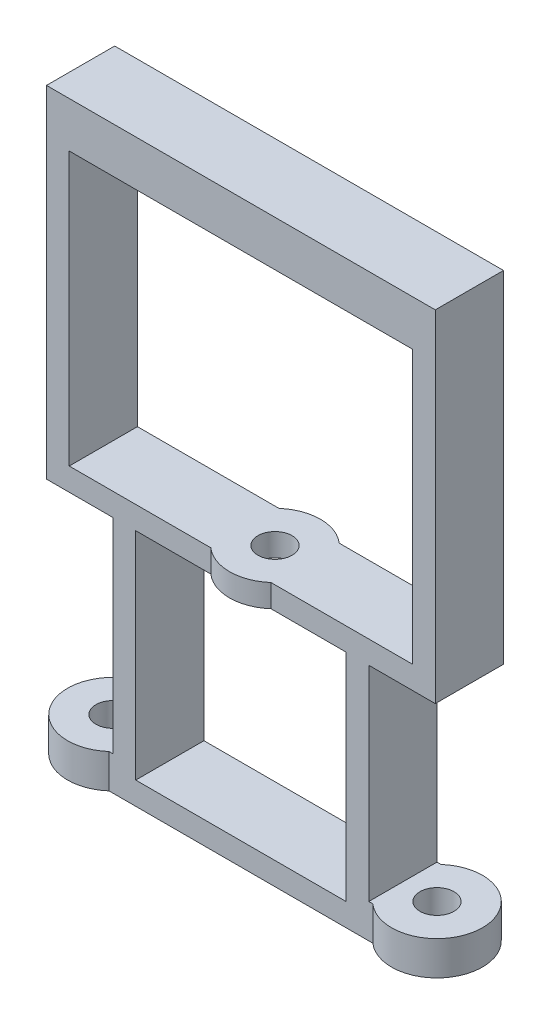
SolidWorks part; units mm, degrees
ref_plane "Front Plane" through (0, 0, 0) normal (0, 0, 1) x (1, 0, 0)
ref_plane "Top Plane" through (0, 0, 0) normal (0, 1, 0) x (1, 0, 0)
ref_plane "Right Plane" through (0, 0, 0) normal (1, 0, 0) x (0, 0, -1)
sketch "Sketch1" plane through (0, 0, 0) normal (0, 1, 0) x (1, 0, 0)
  line L0 (0, 0) -> (1.5, 0)
  line L1 (-55, 0) -> (55, 0) construction
  line L3 (2.6458, 3) -> (25.8542, 3)
  line L4 (27, 0) -> (28.5, 0)
  line L6 (25.8542, -3) -> (2.6458, -3)
  circle A0 centre (0, 0) radius 1.5
  circle A1 centre (28.5, 0) radius 1.5
  arc A2 (2.6458, 3) -> (2.6458, -3) centre (0, 0) ccw
  arc A3 (25.8542, -3) -> (31.1458, 3) centre (28.5, 0) ccw
  arc A4 (25.8542, -3) -> (25.8542, 3) centre (28.5, 0) ccw
  dimension "D2" = 3
  dimension "D3" = 3
  dimension "D5" = 8
  dimension "D8" = 8
  dimension "D1" = 28.5
  dimension "D4" = 6
  dimension "D7" = 3
extrude "Boss-Extrude1" add sketch "Sketch1" along normal blind 3
sketch "Sketch2" plane through (0, 3, 0) normal (0, 1, 0) x (1, 0, 0)
  line L0 (2.6458, 3) -> (25.8542, 3) construction
  line L1 (3, 3) -> (25.5, 3)
  line L2 (3, 3) -> (3, -3)
  line L3 (3, -3) -> (25.5, -3)
  line L4 (25.5, 3) -> (25.5, -3)
  line L5 (25.8542, -3) -> (2.6458, -3) construction
  circle A0 centre (28.5, 0) radius 1.5 construction
  dimension "D1" = 3
  dimension "D2" = 3
extrude "Boss-Extrude2" add sketch "Sketch2" along normal blind 20
sketch "Sketch3" plane through (0, 0, 3) normal (0, 0, 1) x (1, 0, 0)
  line L0 (3, 23) -> (25.5, 23) construction
  line L1 (5, 2) -> (23.5, 2)
  line L2 (5, 2) -> (5, 21)
  line L3 (5, 21) -> (23.5, 21)
  line L4 (23.5, 2) -> (23.5, 21)
  line L5 (3, 23) -> (3, 3) construction
  line L6 (25.5, 23) -> (25.5, 3) construction
  line L7 (25.8542, 3) -> (25.5, 3) construction
  dimension "D1" = 2
  dimension "D2" = 2
  dimension "D3" = 2
  dimension "D4" = 1
extrude "Cut-Extrude1" cut sketch "Sketch3" against normal blind 10
sketch "Sketch4" plane through (0, 23, 0) normal (0, 1, 0) x (1, 0, 0)
  line L0 (16.8958, 3) -> (29.35, 3)
  line L1 (-55, 0) -> (55, 0) construction
  line L2 (16.8958, -3) -> (29.35, -3)
  line L3 (-0.85, 0) -> (-0.85, 3)
  line L4 (25.5, 3) -> (3, 3) construction
  line L5 (-0.85, 3) -> (-0.85, -3)
  line L6 (3, -3) -> (25.5, -3) construction
  line L7 (-0.85, -3) -> (11.6042, -3)
  line L8 (29.35, -3) -> (29.35, 0)
  line L9 (-0.85, 3) -> (11.6042, 3)
  line L10 (29.35, 3) -> (29.35, 0)
  line L11 (3, 3) -> (3, -3) construction
  arc A0 (11.6042, -3) -> (16.8958, -3) centre (14.25, 0) ccw
  arc A1 (16.8958, 3) -> (11.6042, 3) centre (14.25, 0) ccw
  line M1 (3, 3) -> (3, -3)
  line M2 (3, -3) -> (25.5, -3)
  line M3 (25.5, -3) -> (25.5, 3)
  line M4 (25.5, 3) -> (3, 3)
  dimension "D3" = 8
  dimension "D1" = 30.2
  dimension "D2" = 3.85
  dimension "D4" = 15.1
extrude "Boss-Extrude3" add sketch "Sketch4" against normal blind 2 contours L9 L3 L5 L7 M1 | M4 M1 M2 M3 | L10 L9 L7 L8 M3
sketch "Sketch5" plane through (0, 23, 0) normal (0, 1, 0) x (1, 0, 0)
  line L0 (-55, 0) -> (55, 0) construction
  line L1 (29.35, 3) -> (29.35, -3) construction
  circle A0 centre (14.25, 0) radius 1.5
  dimension "D1" = 3
  dimension "D2" = 15.1
extrude "Cut-Extrude2" cut sketch "Sketch5" against normal blind 2
sketch "Sketch6" plane through (-0.85, 0, 0) normal (-1, 0, 0) x (0, 0, 1)
  line L1 (-3, 23) -> (3, 23)
  line L2 (-3, 23) -> (-3, 21)
  line L3 (-3, 21) -> (3, 21)
  line L4 (3, 23) -> (3, 21)
extrude "Boss-Extrude4" add sketch "Sketch6" along normal blind 2
sketch "Sketch7" plane through (0, 23, 0) normal (0, 1, 0) x (1, 0, 0)
  line L0 (29.35, 3) -> (16.8958, 3) construction
  line L1 (-2.85, -3) -> (-0.85, -3)
  line L2 (-2.85, -3) -> (-2.85, 3)
  line L3 (-2.85, 3) -> (-0.85, 3)
  line L4 (-0.85, -3) -> (-0.85, 3)
extrude "Boss-Extrude5" add sketch "Sketch7" along normal blind 28
sketch "Sketch8" plane through (29.35, 0, 0) normal (1, 0, 0) x (0, 0, -1)
  line L1 (-3, 21) -> (3, 21)
  line L2 (-3, 21) -> (-3, 23)
  line L3 (-3, 23) -> (3, 23)
  line L4 (3, 21) -> (3, 23)
extrude "Boss-Extrude6" add sketch "Sketch8" along normal blind 2
sketch "Sketch9" plane through (0, 23, 0) normal (0, 1, 0) x (1, 0, 0)
  line L0 (-0.85, -3) -> (11.6042, -3) construction
  line L1 (31.35, 3) -> (29.35, 3)
  line L2 (31.35, 3) -> (31.35, -3)
  line L3 (31.35, -3) -> (29.35, -3)
  line L4 (29.35, 3) -> (29.35, -3)
  dimension "D1" = 2
extrude "Boss-Extrude7" add sketch "Sketch9" along normal blind 28
sketch "Sketch11" plane through (29.35, 0, 0) normal (-1, 0, 0) x (0, 0, 1)
  line L0 (3, 51) -> (3, 23) construction
  line L1 (-3, 51) -> (3, 51)
  line L2 (-3, 51) -> (-3, 47)
  line L3 (-3, 47) -> (3, 47)
  line L4 (3, 51) -> (3, 47)
  dimension "D1" = 4
extrude "Boss-Extrude8" add sketch "Sketch11" along normal blind 31
